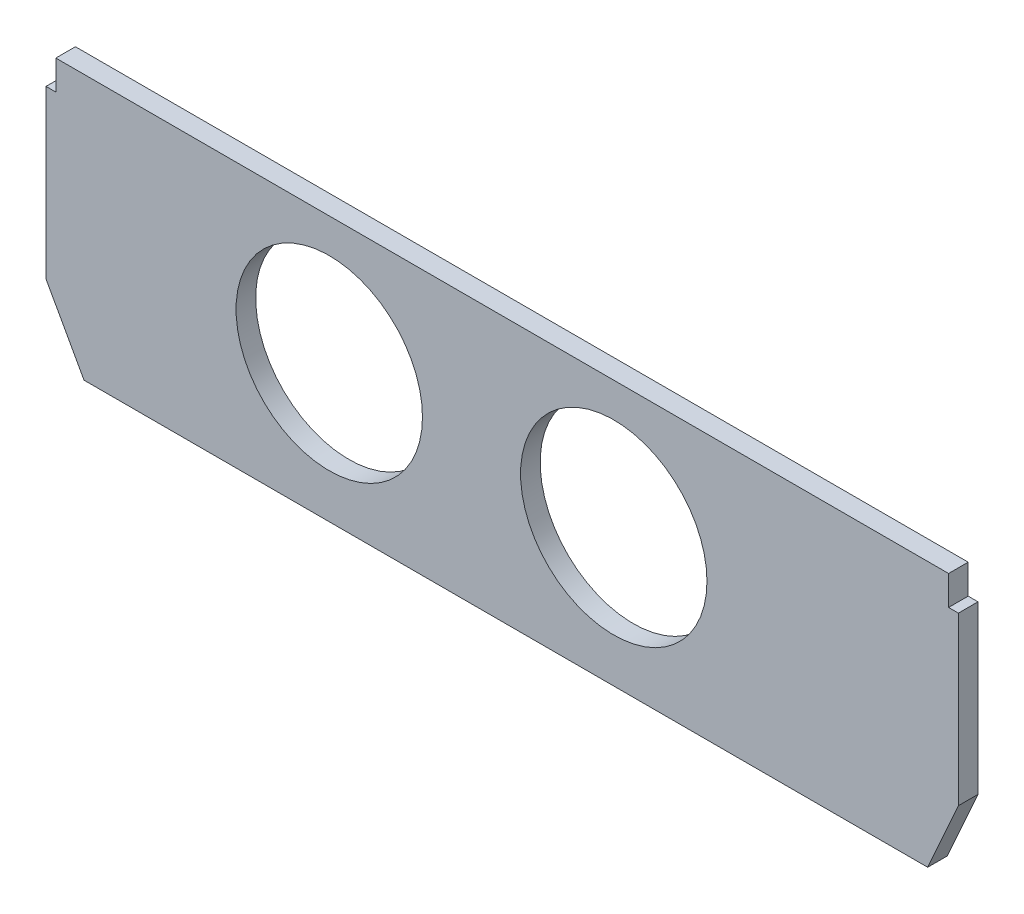
SolidWorks part; units mm, degrees
ref_plane "Front Plane" through (0, 0, 0) normal (0, 0, 1) x (1, 0, 0)
ref_plane "Top Plane" through (0, 0, 0) normal (0, 1, 0) x (1, 0, 0)
ref_plane "Right Plane" through (0, 0, 0) normal (1, 0, 0) x (0, 0, -1)
sketch "Sketch2" plane through (0, 0, 0) normal (0, 0, 1) x (1, 0, 0)
  line L0 (0, 0) -> (-430, 0)
  line L1 (-430, 0) -> (-449.3649, 35)
  line L2 (-449.3649, 35) -> (-449.3649, 120)
  line L3 (-449.3649, 120) -> (-444.3649, 120)
  line L4 (-444.3649, 120) -> (-444.3649, 135)
  line L5 (0, 0) -> (15.6351, 35)
  line L6 (15.6351, 35) -> (15.6351, 120)
  line L7 (15.6351, 120) -> (10.6351, 120)
  line L8 (10.6351, 120) -> (10.6351, 135)
  line L9 (10.6351, 135) -> (-444.3649, 135)
  circle A0 centre (-305, 70) radius 60
  circle A1 centre (-305, 70) radius 47.5
  circle A2 centre (-160, 70) radius 60
  circle A3 centre (-160, 70) radius 47.5
  dimension "D11" = 120
  dimension "D12" = 95
  dimension "D13" = 120
  dimension "D14" = 95
  dimension "D1" = 430
  dimension "D2" = 35
  dimension "D3" = 85
  dimension "D4" = 35
  dimension "D5" = 85
  dimension "D6" = 5
  dimension "D7" = 5
  dimension "D8" = 15
  dimension "D9" = 455
  dimension "D10" = 40
  dimension "D15" = 125
  dimension "D16" = 160
  dimension "D17" = 65
  dimension "D18" = 65
extrude "Boss-Extrude2" add sketch "Sketch2" along normal blind 10 contours L8 L9 L4 L3 L2 L1 L0 L5 L6 L7 A2 A0 | A2 A3 | A0 A1
